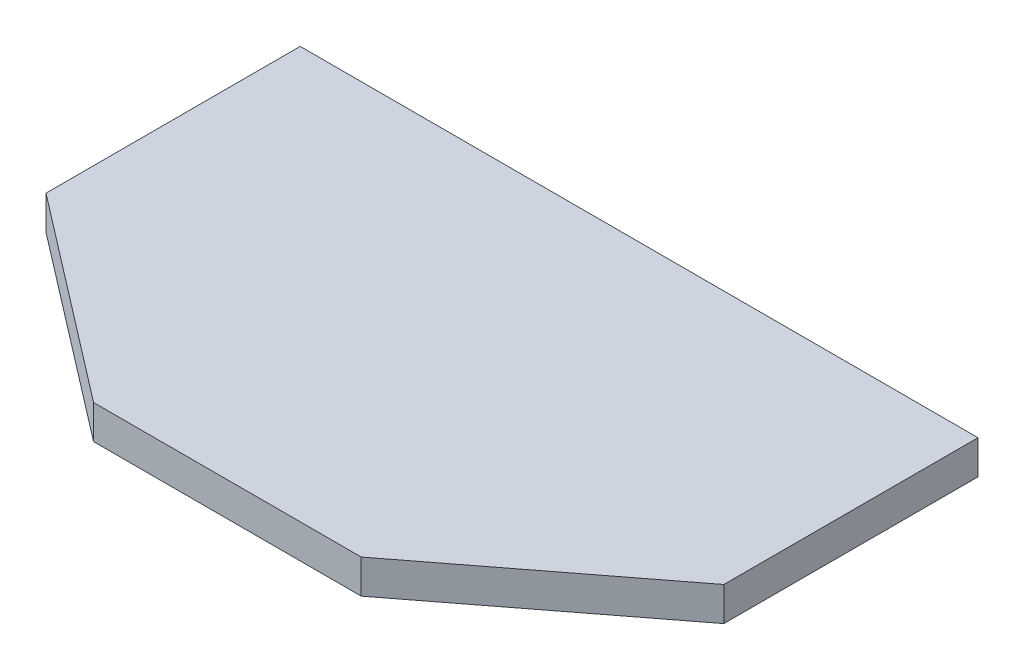
SolidWorks part; units mm, degrees
ref_plane "Front Plane" through (0, 0, 0) normal (0, 0, 1) x (1, 0, 0)
ref_plane "Top Plane" through (0, 0, 0) normal (0, 1, 0) x (1, 0, 0)
ref_plane "Right Plane" through (0, 0, 0) normal (1, 0, 0) x (0, 0, -1)
sketch "Sketch1" plane through (0, 0, 0) normal (0, 1, 0) x (1, 0, 0)
  line L0 (0, 0) -> (-10.0296, 0)
  line L1 (0, 0) -> (10.0296, 0)
  line L2 (0, 11.1541) -> (0, -9.7975) construction
  line L3 (-25.4, 19.05) -> (-25.4, 11.806)
  line L4 (25.4, 19.05) -> (25.4, 11.806)
  line L5 (-25.4, 11.806) -> (-10.0296, 0)
  line L6 (25.4, 11.806) -> (10.0296, 0)
  line L7 (-25.4, 19.05) -> (-25.4, 30.856)
  line L8 (-25.4, 30.856) -> (25.4, 30.856)
  line L9 (25.4, 30.856) -> (25.4, 19.05)
  dimension "D1" = 19.05
  dimension "D2" = 19.3812
  dimension "D5" = 25.4
extrude "Boss-Extrude1" add sketch "Sketch1" against normal blind 2.54
sketch "Sketch2" plane through (0, 0, 0) normal (0, 1, 0) x (1, 0, 0)
  circle A1 centre (3.2455, 5.5413) radius 1 construction
  circle A2 centre (3.2455, 5.5413) radius 1 construction
  circle A3 centre (3.2455, 5.5413) radius 1.27
  circle A4 centre (1.6228, 10.2707) radius 1 construction
  circle A5 centre (1.6228, 10.2707) radius 1 construction
  circle A6 centre (1.6228, 10.2707) radius 1.27
  dimension "D1" = 2.54
extrude "Cut-Extrude1" [suppressed] cut sketch "Sketch2" against normal through all and the other way through all
